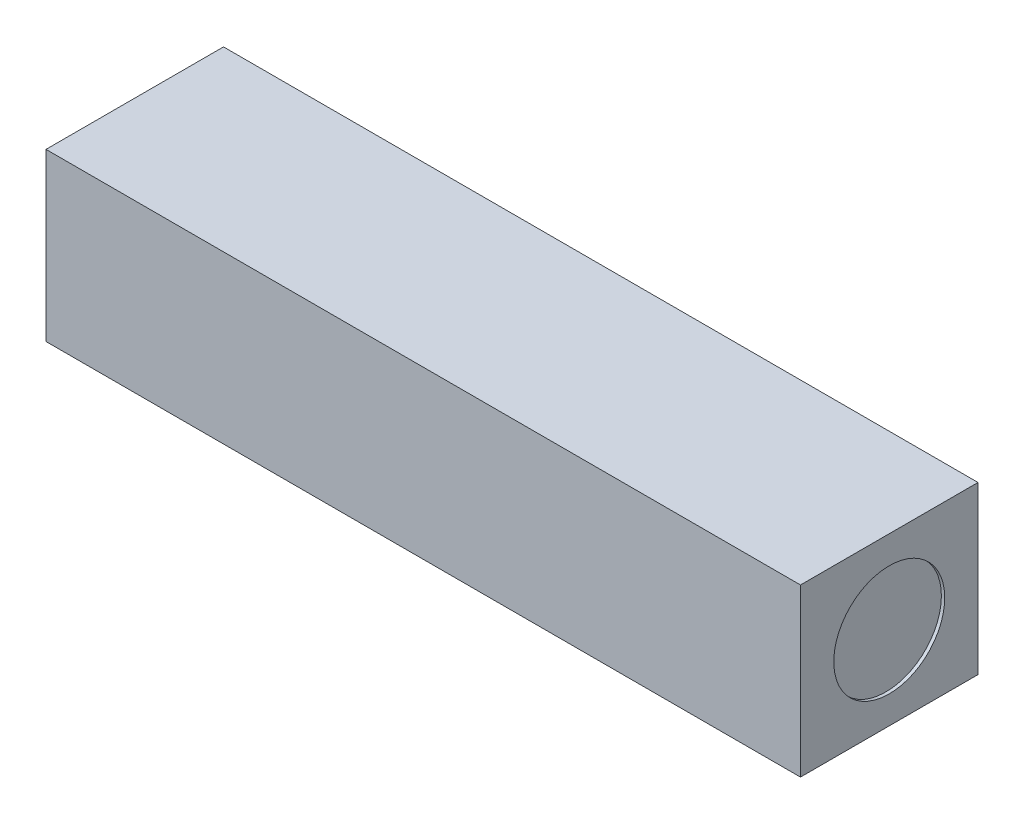
SolidWorks part; units mm, degrees
ref_plane "Front Plane" through (0, 0, 0) normal (0, 0, 1) x (1, 0, 0)
ref_plane "Top Plane" through (0, 0, 0) normal (0, 1, 0) x (1, 0, 0)
ref_plane "Right Plane" through (0, 0, 0) normal (1, 0, 0) x (0, 0, -1)
sketch "Croquis1" plane through (0, 0, 0) normal (0, 1, 0) x (1, 0, 0)
  line L0 (-17, -4) -> (-17, 4)
  line L1 (-17, -4) -> (17, -4)
  line L2 (-17, 4) -> (17, 4)
  line L3 (17, -4) -> (17, 4)
  line L4 (-17, -4) -> (17, 4) construction
  line L5 (-17, 4) -> (17, -4) construction
  point P1 (0, 0)
  dimension "D1" = 8
  dimension "D2" = 34
extrude "Saliente-Extruir1" add sketch "Croquis1" along normal blind 7.5
sketch "Croquis2" plane through (17, 0, 0) normal (1, 0, 0) x (0, 0, -1)
  circle A0 centre (0, 3.75) radius 2.5
  dimension "D1" = 5
extrude "Cortar-Extruir1" cut sketch "Croquis2" against normal blind 0.15
